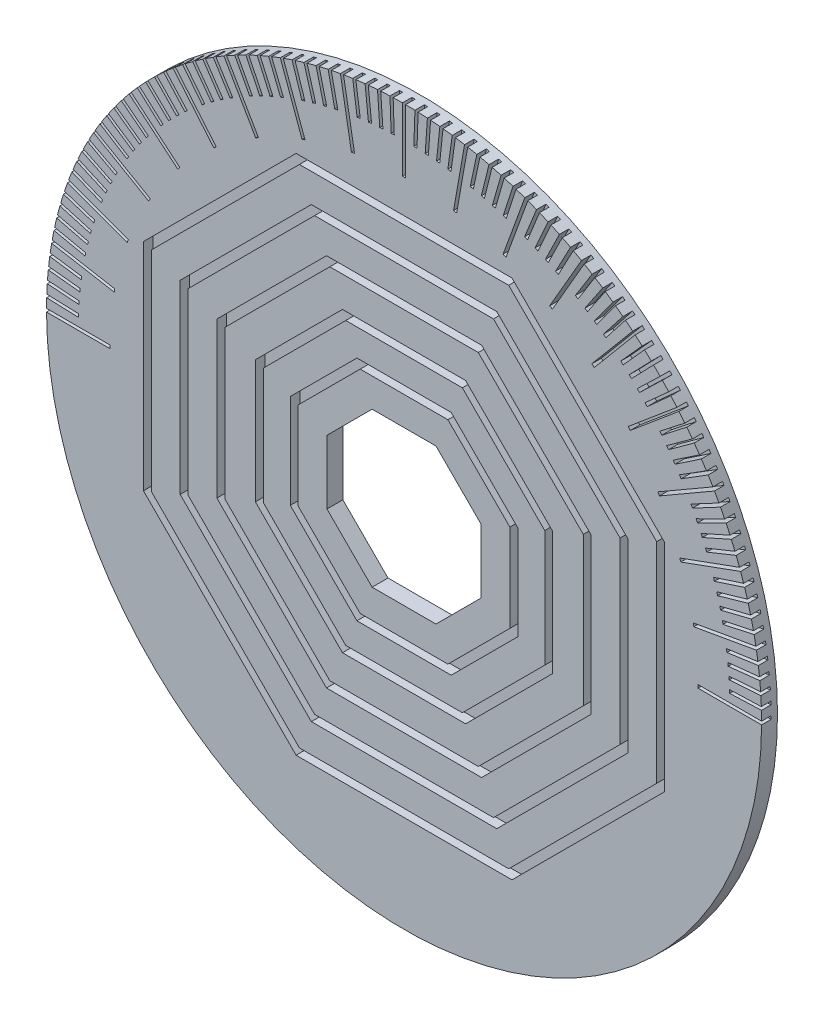
SolidWorks part; units mm, degrees
ref_plane "정면" through (0, 0, 0) normal (0, 0, 1) x (1, 0, 0)
ref_plane "윗면" through (0, 0, 0) normal (0, 1, 0) x (1, 0, 0)
ref_plane "우측면" through (0, 0, 0) normal (1, 0, 0) x (0, 0, -1)
sketch "스케치1" plane through (0, 0, 0) normal (0, 0, 1) x (1, 0, 0)
  circle A0 centre (0, 0) radius 45
  dimension "D1" = 90
extrude "보스-돌출1" add sketch "스케치1" along normal blind 2
sketch "스케치2" plane through (0, 0, 2) normal (0, 0, 1) x (1, 0, 0)
  line L1 (-13.5853, 32.7977) -> (-32.7977, 13.5853)
  line L2 (-32.7977, 13.5853) -> (-32.7977, -13.5853)
  line L3 (-32.7977, -13.5853) -> (-13.5853, -32.7977)
  line L4 (-13.5853, -32.7977) -> (13.5853, -32.7977)
  line L5 (13.5853, -32.7977) -> (32.7977, -13.5853)
  line L6 (32.7977, -13.5853) -> (32.7977, 13.5853)
  line L7 (32.7977, 13.5853) -> (13.5853, 32.7977)
  line L8 (13.5853, 32.7977) -> (-13.5853, 32.7977)
  line L9 (-13.171, 31.7977) -> (-31.7977, 13.171)
  line L10 (-31.7977, 13.171) -> (-31.7977, -13.171)
  line L11 (-31.7977, -13.171) -> (-13.171, -31.7977)
  line L12 (-13.171, -31.7977) -> (13.171, -31.7977)
  line L13 (13.171, -31.7977) -> (31.7977, -13.171)
  line L14 (31.7977, -13.171) -> (31.7977, 13.171)
  line L15 (31.7977, 13.171) -> (13.171, 31.7977)
  line L16 (13.171, 31.7977) -> (-13.171, 31.7977)
  line L18 (55, 0) -> (-55, 0) construction
  circle A0 centre (0, 0) radius 35.5 construction
  dimension "D1" = 71
  dimension "D2" = 1
extrude "컷-돌출1" cut sketch "스케치2" against normal blind 1.2 contours L7 L8 L1 L2 L3 L4 L5 L6 L16 L15 L14 L13 L12 L11 L10 L9
sketch "스케치3" plane through (0, 0, 2) normal (0, 0, 1) x (1, 0, 0)
  line L8 (-31.7977, 13.171) -> (-31.7977, -13.171) construction
  line L9 (11.6718, -28.1783) -> (28.1783, -11.6718)
  line L10 (28.1783, -11.6718) -> (28.1783, 11.6718)
  line L11 (28.1783, 11.6718) -> (11.6718, 28.1783)
  line L12 (11.6718, 28.1783) -> (-11.6718, 28.1783)
  line L13 (-11.6718, 28.1783) -> (-28.1783, 11.6718)
  line L14 (-28.1783, 11.6718) -> (-28.1783, -11.6718)
  line L15 (-28.1783, -11.6718) -> (-11.6718, -28.1783)
  line L16 (-11.6718, -28.1783) -> (11.6718, -28.1783)
  line L17 (11.2576, -27.1783) -> (27.1783, -11.2576)
  line L18 (-9.7584, 23.5589) -> (-23.5589, 9.7584)
  line L19 (-23.5589, 9.7584) -> (-23.5589, -9.7584)
  line L20 (-23.5589, -9.7584) -> (-9.7584, -23.5589)
  line L21 (-9.7584, -23.5589) -> (9.7584, -23.5589)
  line L22 (9.7584, -23.5589) -> (23.5589, -9.7584)
  line L23 (23.5589, -9.7584) -> (23.5589, 9.7584)
  line L24 (23.5589, 9.7584) -> (9.7584, 23.5589)
  line L25 (9.7584, 23.5589) -> (-9.7584, 23.5589)
  line L26 (-7.7493, 18.7086) -> (-18.7086, 7.7493)
  line L27 (-18.7086, 7.7493) -> (-18.7086, -7.7493)
  line L28 (-18.7086, -7.7493) -> (-7.7493, -18.7086)
  line L29 (-7.7493, -18.7086) -> (7.7493, -18.7086)
  line L30 (7.7493, -18.7086) -> (18.7086, -7.7493)
  line L31 (18.7086, -7.7493) -> (18.7086, 7.7493)
  line L32 (18.7086, 7.7493) -> (7.7493, 18.7086)
  line L33 (7.7493, 18.7086) -> (-7.7493, 18.7086)
  line L34 (5.9316, -14.3201) -> (14.3201, -5.9316)
  line L35 (14.3201, -5.9316) -> (14.3201, 5.9316)
  line L36 (14.3201, 5.9316) -> (5.9316, 14.3201)
  line L37 (5.9316, 14.3201) -> (-5.9316, 14.3201)
  line L38 (-5.9316, 14.3201) -> (-14.3201, 5.9316)
  line L39 (-14.3201, 5.9316) -> (-14.3201, -5.9316)
  line L40 (-14.3201, -5.9316) -> (-5.9316, -14.3201)
  line L41 (-5.9316, -14.3201) -> (5.9316, -14.3201)
  line L42 (9.7007, -4.0182) -> (9.7007, 4.0182)
  line L43 (9.7007, 4.0182) -> (4.0182, 9.7007)
  line L44 (4.0182, 9.7007) -> (-4.0182, 9.7007)
  line L45 (-4.0182, 9.7007) -> (-9.7007, 4.0182)
  line L46 (-9.7007, 4.0182) -> (-9.7007, -4.0182)
  line L47 (-9.7007, -4.0182) -> (-4.0182, -9.7007)
  line L48 (-4.0182, -9.7007) -> (4.0182, -9.7007)
  line L49 (4.0182, -9.7007) -> (9.7007, -4.0182)
  line L50 (27.1783, -11.2576) -> (27.1783, 11.2576)
  line L51 (27.1783, 11.2576) -> (11.2576, 27.1783)
  line L52 (11.2576, 27.1783) -> (-11.2576, 27.1783)
  line L53 (-11.2576, 27.1783) -> (-27.1783, 11.2576)
  line L54 (-27.1783, 11.2576) -> (-27.1783, -11.2576)
  line L55 (-27.1783, -11.2576) -> (-11.2576, -27.1783)
  line L56 (-11.2576, -27.1783) -> (11.2576, -27.1783)
  line L57 (-9.3442, 22.5589) -> (-22.5589, 9.3442)
  line L58 (-22.5589, 9.3442) -> (-22.5589, -9.3442)
  line L59 (-22.5589, -9.3442) -> (-9.3442, -22.5589)
  line L60 (-9.3442, -22.5589) -> (9.3442, -22.5589)
  line L61 (9.3442, -22.5589) -> (22.5589, -9.3442)
  line L62 (22.5589, -9.3442) -> (22.5589, 9.3442)
  line L63 (22.5589, 9.3442) -> (9.3442, 22.5589)
  line L64 (9.3442, 22.5589) -> (-9.3442, 22.5589)
  line L65 (-7.3351, 17.7086) -> (-17.7086, 7.3351)
  line L66 (-17.7086, 7.3351) -> (-17.7086, -7.3351)
  line L67 (-17.7086, -7.3351) -> (-7.3351, -17.7086)
  line L68 (-7.3351, -17.7086) -> (7.3351, -17.7086)
  line L69 (7.3351, -17.7086) -> (17.7086, -7.3351)
  line L70 (17.7086, -7.3351) -> (17.7086, 7.3351)
  line L71 (17.7086, 7.3351) -> (7.3351, 17.7086)
  line L72 (7.3351, 17.7086) -> (-7.3351, 17.7086)
  line L73 (5.5174, -13.3201) -> (13.3201, -5.5174)
  line L74 (13.3201, -5.5174) -> (13.3201, 5.5174)
  line L75 (13.3201, 5.5174) -> (5.5174, 13.3201)
  line L76 (5.5174, 13.3201) -> (-5.5174, 13.3201)
  line L77 (-5.5174, 13.3201) -> (-13.3201, 5.5174)
  line L78 (-13.3201, 5.5174) -> (-13.3201, -5.5174)
  line L79 (-13.3201, -5.5174) -> (-5.5174, -13.3201)
  line L80 (-5.5174, -13.3201) -> (5.5174, -13.3201)
  circle A0 centre (0, 0) radius 30.5 construction
  circle A1 centre (0, 0) radius 25.5 construction
  circle A2 centre (0, 0) radius 20.25 construction
  circle A3 centre (0, 0) radius 15.5 construction
  circle A4 centre (0, 0) radius 10.5 construction
  dimension "D1" = 61
  dimension "51" = 51
  dimension "D3" = 40.5
  dimension "D4" = 31
  dimension "D5" = 21
  dimension "D6" = 1
  dimension "D7" = 1
  dimension "D8" = 1
  dimension "D9" = 1
extrude "컷-돌출2" cut sketch "스케치3" against normal blind 1.2 contours L15 L16 L9 L10 L11 L12 L13 L14 L56 L55 L54 L53 L52 L51 L50 L17 | L24 L25 L18 L19 L20 L21 L22 L23 L64 L63 L62 L61 L60 L59 L58 L57 | L32 L33 L26 L27 L28 L29 L30 L31 L72 L71 L70 L69 L68 L67 L66 L65 | L40 L41 L34 L35 L36 L37 L38 L39 L80 L79 L78 L77 L76 L75 L74 L73 | L45 L46 L47 L48 L49 L42 L43 L44
sketch "스케치4" plane through (0, 0, 2) normal (0, 0, 1) x (1, 0, 0)
  line L75 (-32.7977, 13.5853) -> (-32.7977, -13.5853) construction
  line L76 (-45, 0.2) -> (-37, 0.2)
  line L77 (-45, 0.2) -> (-45, -0.2)
  line L78 (-45, -0.2) -> (-37, -0.2)
  line L79 (-37, 0.2) -> (-37, -0.2)
  line L80 (-45, 0) -> (-37, 0) construction
  line L81 (-44.2816, 8.0111) -> (-44.3511, 7.6172)
  line L82 (1.1, 0) -> (-1.1, 0) construction
  line L83 (-44.2816, 8.0111) -> (-36.4032, 6.6219)
  line L84 (-36.4032, 6.6219) -> (-36.4726, 6.228)
  line L85 (-44.3511, 7.6172) -> (-36.4726, 6.228)
  line L86 (-44.3163, 7.8142) -> (-36.4379, 6.425) construction
  line L87 (-42.2178, 15.5788) -> (-42.3546, 15.203)
  line L88 (-42.2178, 15.5788) -> (-34.7002, 12.8427)
  line L89 (-34.7002, 12.8427) -> (-34.837, 12.4668)
  line L90 (-42.3546, 15.203) -> (-34.837, 12.4668)
  line L91 (-42.2862, 15.3909) -> (-34.7686, 12.6547) construction
  line L92 (-38.8711, 22.6732) -> (-39.0711, 22.3268)
  line L93 (-38.8711, 22.6732) -> (-31.9429, 18.6732)
  line L94 (-31.9429, 18.6732) -> (-32.1429, 18.3268)
  line L95 (-39.0711, 22.3268) -> (-32.1429, 18.3268)
  line L96 (-38.9711, 22.5) -> (-32.0429, 18.5) construction
  line L97 (-34.3434, 29.0787) -> (-34.6006, 28.7722)
  line L98 (-34.3434, 29.0787) -> (-28.2151, 23.9364)
  line L99 (-28.2151, 23.9364) -> (-28.4722, 23.6299)
  line L100 (-34.6006, 28.7722) -> (-28.4722, 23.6299)
  line L101 (-34.472, 28.9254) -> (-28.3436, 23.7831) construction
  line L102 (-28.7722, 34.6006) -> (-29.0787, 34.3434)
  line L103 (-28.7722, 34.6006) -> (-23.6299, 28.4722)
  line L104 (-23.6299, 28.4722) -> (-23.9364, 28.2151)
  line L105 (-29.0787, 34.3434) -> (-23.9364, 28.2151)
  line L106 (-28.9254, 34.472) -> (-23.7831, 28.3436) construction
  line L107 (-22.3268, 39.0711) -> (-22.6732, 38.8711)
  line L108 (-22.3268, 39.0711) -> (-18.3268, 32.1429)
  line L109 (-18.3268, 32.1429) -> (-18.6732, 31.9429)
  line L110 (-22.6732, 38.8711) -> (-18.6732, 31.9429)
  line L111 (-22.5, 38.9711) -> (-18.5, 32.0429) construction
  line L112 (-15.203, 42.3546) -> (-15.5788, 42.2178)
  line L113 (-15.203, 42.3546) -> (-12.4668, 34.837)
  line L114 (-12.4668, 34.837) -> (-12.8427, 34.7002)
  line L115 (-15.5788, 42.2178) -> (-12.8427, 34.7002)
  line L116 (-15.3909, 42.2862) -> (-12.6547, 34.7686) construction
  line L117 (-7.6172, 44.3511) -> (-8.0111, 44.2816)
  line L118 (-7.6172, 44.3511) -> (-6.228, 36.4726)
  line L119 (-6.228, 36.4726) -> (-6.6219, 36.4032)
  line L120 (-8.0111, 44.2816) -> (-6.6219, 36.4032)
  line L121 (-7.8142, 44.3163) -> (-6.425, 36.4379) construction
  line L122 (0.2, 45) -> (-0.2, 45)
  line L123 (0.2, 45) -> (0.2, 37)
  line L124 (0.2, 37) -> (-0.2, 37)
  line L125 (-0.2, 45) -> (-0.2, 37)
  line L126 (0, 45) -> (0, 37) construction
  line L127 (8.0111, 44.2816) -> (7.6172, 44.3511)
  line L128 (8.0111, 44.2816) -> (6.6219, 36.4032)
  line L129 (6.6219, 36.4032) -> (6.228, 36.4726)
  line L130 (7.6172, 44.3511) -> (6.228, 36.4726)
  line L131 (7.8142, 44.3163) -> (6.425, 36.4379) construction
  line L132 (15.5788, 42.2178) -> (15.203, 42.3546)
  line L133 (15.5788, 42.2178) -> (12.8427, 34.7002)
  line L134 (12.8427, 34.7002) -> (12.4668, 34.837)
  line L135 (15.203, 42.3546) -> (12.4668, 34.837)
  line L136 (15.3909, 42.2862) -> (12.6547, 34.7686) construction
  line L137 (22.6732, 38.8711) -> (22.3268, 39.0711)
  line L138 (22.6732, 38.8711) -> (18.6732, 31.9429)
  line L139 (18.6732, 31.9429) -> (18.3268, 32.1429)
  line L140 (22.3268, 39.0711) -> (18.3268, 32.1429)
  line L141 (22.5, 38.9711) -> (18.5, 32.0429) construction
  line L142 (29.0787, 34.3434) -> (28.7722, 34.6006)
  line L143 (29.0787, 34.3434) -> (23.9364, 28.2151)
  line L144 (23.9364, 28.2151) -> (23.6299, 28.4722)
  line L145 (28.7722, 34.6006) -> (23.6299, 28.4722)
  line L146 (28.9254, 34.472) -> (23.7831, 28.3436) construction
  line L147 (34.6006, 28.7722) -> (34.3434, 29.0787)
  line L148 (34.6006, 28.7722) -> (28.4722, 23.6299)
  line L149 (28.4722, 23.6299) -> (28.2151, 23.9364)
  line L150 (34.3434, 29.0787) -> (28.2151, 23.9364)
  line L151 (34.472, 28.9254) -> (28.3436, 23.7831) construction
  line L152 (39.0711, 22.3268) -> (38.8711, 22.6732)
  line L153 (39.0711, 22.3268) -> (32.1429, 18.3268)
  line L154 (32.1429, 18.3268) -> (31.9429, 18.6732)
  line L155 (38.8711, 22.6732) -> (31.9429, 18.6732)
  line L156 (38.9711, 22.5) -> (32.0429, 18.5) construction
  line L157 (42.3546, 15.203) -> (42.2178, 15.5788)
  line L158 (42.3546, 15.203) -> (34.837, 12.4668)
  line L159 (34.837, 12.4668) -> (34.7002, 12.8427)
  line L160 (42.2178, 15.5788) -> (34.7002, 12.8427)
  line L161 (42.2862, 15.3909) -> (34.7686, 12.6547) construction
  line L162 (44.3511, 7.6172) -> (44.2816, 8.0111)
  line L163 (44.3511, 7.6172) -> (36.4726, 6.228)
  line L164 (36.4726, 6.228) -> (36.4032, 6.6219)
  line L165 (44.2816, 8.0111) -> (36.4032, 6.6219)
  line L166 (44.3163, 7.8142) -> (36.4379, 6.425) construction
  line L167 (45, -0.2) -> (45, 0.2)
  line L168 (45, -0.2) -> (37, -0.2)
  line L169 (37, -0.2) -> (37, 0.2)
  line L170 (45, 0.2) -> (37, 0.2)
  line L171 (45, 0) -> (37, 0) construction
  point P115 (-2.3849, 0)
  point P122 (0, 0)
  dimension "D1" = 8
  dimension "D2" = 0.4
  dimension "D3" = 45
sketch "스케치6" plane through (0, 0, 2) normal (0, 0, 1) x (1, 0, 0)
  line L0 (-32.7977, 13.5853) -> (-32.7977, -13.5853) construction
  line L1 (-45, 0.2) -> (-41, 0.2)
  line L2 (-45, 0.2) -> (-45, -0.2)
  line L3 (-45, -0.2) -> (-41, -0.2)
  line L4 (-41, 0.2) -> (-41, -0.2)
  line L5 (-45, 0) -> (-41, 0) construction
  line L7 (1.1, 0) -> (-1.1, 0) construction
  line L476 (-44.9656, 1.7704) -> (-44.9796, 1.3706)
  line L501 (-44.9656, 1.7704) -> (-40.968, 1.6308)
  line L526 (-40.968, 1.6308) -> (-40.982, 1.231)
  line L551 (-44.9796, 1.3706) -> (-40.982, 1.231)
  line L576 (-44.9726, 1.5705) -> (-40.975, 1.4309) construction
  line L601 (-44.8764, 3.3386) -> (-44.9043, 2.9395)
  line L626 (-44.8764, 3.3386) -> (-40.8862, 3.0595)
  line L651 (-40.8862, 3.0595) -> (-40.9141, 2.6605)
  line L676 (-44.9043, 2.9395) -> (-40.9141, 2.6605)
  line L701 (-44.8904, 3.139) -> (-40.9001, 2.86) construction
  line L726 (-44.7326, 4.9027) -> (-44.7744, 4.5049)
  line L751 (-44.7326, 4.9027) -> (-40.7545, 4.4846)
  line L776 (-40.7545, 4.4846) -> (-40.7963, 4.0868)
  line L801 (-44.7744, 4.5049) -> (-40.7963, 4.0868)
  line L826 (-44.7535, 4.7038) -> (-40.7754, 4.2857) construction
  line L851 (-44.5342, 6.4608) -> (-44.5899, 6.0647)
  line L876 (-44.5342, 6.4608) -> (-40.5732, 5.9042)
  line L901 (-40.5732, 5.9042) -> (-40.6288, 5.508)
  line L906 (-44.5899, 6.0647) -> (-40.6288, 5.508)
  line L911 (-44.5621, 6.2628) -> (-40.601, 5.7061) construction
  line L916 (-44.2816, 8.0111) -> (-44.3511, 7.6172)
  line L921 (-44.2816, 8.0111) -> (-40.3424, 7.3165)
  line L926 (-40.3424, 7.3165) -> (-40.4118, 6.9226)
  line L931 (-44.3511, 7.6172) -> (-40.4118, 6.9226)
  line L936 (-44.3163, 7.8142) -> (-40.3771, 7.1196) construction
  line L941 (-43.9751, 9.5517) -> (-44.0582, 9.1604)
  line L946 (-43.9751, 9.5517) -> (-40.0625, 8.72)
  line L951 (-40.0625, 8.72) -> (-40.1456, 8.3287)
  line L956 (-44.0582, 9.1604) -> (-40.1456, 8.3287)
  line L961 (-44.0166, 9.356) -> (-40.1041, 8.5244) construction
  line L966 (-43.6149, 11.0805) -> (-43.7117, 10.6924)
  line L971 (-43.6149, 11.0805) -> (-39.7337, 10.1129)
  line L976 (-39.7337, 10.1129) -> (-39.8305, 9.7247)
  line L981 (-43.7117, 10.6924) -> (-39.8305, 9.7247)
  line L986 (-43.6633, 10.8865) -> (-39.7821, 9.9188) construction
  line L991 (-43.2016, 12.5959) -> (-43.3119, 12.2114)
  line L996 (-43.2016, 12.5959) -> (-39.3566, 11.4934)
  line L1001 (-39.3566, 11.4934) -> (-39.4669, 11.1089)
  line L1006 (-43.3119, 12.2114) -> (-39.4669, 11.1089)
  line L1011 (-43.2568, 12.4037) -> (-39.4117, 11.3011) construction
  line L1016 (-42.7357, 14.096) -> (-42.8593, 13.7156)
  line L1021 (-42.7357, 14.096) -> (-38.9315, 12.8599)
  line L1026 (-38.9315, 12.8599) -> (-39.0551, 12.4795)
  line L1031 (-42.8593, 13.7156) -> (-39.0551, 12.4795)
  line L1036 (-42.7975, 13.9058) -> (-38.9933, 12.6697) construction
  line L1041 (-42.2178, 15.5788) -> (-42.3546, 15.203)
  line L1046 (-42.2178, 15.5788) -> (-38.459, 14.2108)
  line L1051 (-38.459, 14.2108) -> (-38.5958, 13.8349)
  line L1056 (-42.3546, 15.203) -> (-38.5958, 13.8349)
  line L1061 (-42.2862, 15.3909) -> (-38.5274, 14.0228) construction
  line L1066 (-41.6484, 17.0427) -> (-41.7982, 16.6719)
  line L1071 (-41.6484, 17.0427) -> (-37.9396, 15.5443)
  line L1076 (-37.9396, 15.5443) -> (-38.0895, 15.1734)
  line L1081 (-41.7982, 16.6719) -> (-38.0895, 15.1734)
  line L1086 (-41.7233, 16.8573) -> (-38.0145, 15.3589) construction
  line L1091 (-41.0282, 18.4859) -> (-41.1909, 18.1204)
  line L1096 (-41.0282, 18.4859) -> (-37.374, 16.8589)
  line L1101 (-37.374, 16.8589) -> (-37.5367, 16.4935)
  line L1106 (-41.1909, 18.1204) -> (-37.5367, 16.4935)
  line L1111 (-41.1095, 18.3031) -> (-37.4554, 16.6762) construction
  line L1116 (-40.3581, 19.9065) -> (-40.5334, 19.5469)
  line L1121 (-40.3581, 19.9065) -> (-36.7629, 18.153)
  line L1126 (-36.7629, 18.153) -> (-36.9382, 17.7935)
  line L1131 (-40.5334, 19.5469) -> (-36.9382, 17.7935)
  line L1136 (-40.4457, 19.7267) -> (-36.8506, 17.9732) construction
  line L1141 (-39.6387, 21.3028) -> (-39.8265, 20.9496)
  line L1146 (-39.6387, 21.3028) -> (-36.107, 19.4249)
  line L1151 (-36.107, 19.4249) -> (-36.2947, 19.0717)
  line L1156 (-39.8265, 20.9496) -> (-36.2947, 19.0717)
  line L1161 (-39.7326, 21.1262) -> (-36.2009, 19.2483) construction
  line L1166 (-38.8711, 22.6732) -> (-39.0711, 22.3268)
  line L1171 (-38.8711, 22.6732) -> (-35.407, 20.6732)
  line L1176 (-35.407, 20.6732) -> (-35.607, 20.3268)
  line L1181 (-39.0711, 22.3268) -> (-35.607, 20.3268)
  line L1186 (-38.9711, 22.5) -> (-35.507, 20.5) construction
  line L1191 (-38.0562, 24.016) -> (-38.2681, 23.6768)
  line L1196 (-38.0562, 24.016) -> (-34.664, 21.8963)
  line L1201 (-34.664, 21.8963) -> (-34.876, 21.5571)
  line L1206 (-38.2681, 23.6768) -> (-34.876, 21.5571)
  line L1211 (-38.1622, 23.8464) -> (-34.77, 21.7267) construction
  line L1216 (-37.1949, 25.3295) -> (-37.4185, 24.9979)
  line L1221 (-37.1949, 25.3295) -> (-33.8787, 23.0927)
  line L1226 (-33.8787, 23.0927) -> (-34.1024, 22.7611)
  line L1231 (-37.4185, 24.9979) -> (-34.1024, 22.7611)
  line L1236 (-37.3067, 25.1637) -> (-33.9905, 22.9269) construction
  line L1241 (-36.2882, 26.6121) -> (-36.5233, 26.2885)
  line L1246 (-36.2882, 26.6121) -> (-33.0521, 24.261)
  line L1251 (-33.0521, 24.261) -> (-33.2873, 23.9374)
  line L1256 (-36.5233, 26.2885) -> (-33.2873, 23.9374)
  line L1261 (-36.4058, 26.4503) -> (-33.1697, 24.0992) construction
  line L1266 (-35.3374, 27.8624) -> (-35.5836, 27.5472)
  line L1271 (-35.3374, 27.8624) -> (-32.1853, 25.3997)
  line L1276 (-32.1853, 25.3997) -> (-32.4316, 25.0845)
  line L1281 (-35.5836, 27.5472) -> (-32.4316, 25.0845)
  line L1286 (-35.4605, 27.7048) -> (-32.3084, 25.2421) construction
  line L1291 (-34.3434, 29.0787) -> (-34.6006, 28.7722)
  line L1296 (-34.3434, 29.0787) -> (-31.2793, 26.5075)
  line L1301 (-31.2793, 26.5075) -> (-31.5364, 26.2011)
  line L1306 (-34.6006, 28.7722) -> (-31.5364, 26.2011)
  line L1311 (-34.472, 28.9254) -> (-31.4078, 26.3543) construction
  line L1316 (-33.3077, 30.2595) -> (-33.5753, 29.9622)
  line L1321 (-33.3077, 30.2595) -> (-30.3351, 27.583)
  line L1326 (-30.3351, 27.583) -> (-30.6028, 27.2857)
  line L1331 (-33.5753, 29.9622) -> (-30.6028, 27.2857)
  line L1336 (-33.4415, 30.1109) -> (-30.4689, 27.4344) construction
  line L1341 (-32.2314, 31.4035) -> (-32.5092, 31.1158)
  line L1346 (-32.2314, 31.4035) -> (-29.354, 28.6249)
  line L1351 (-29.354, 28.6249) -> (-29.6319, 28.3371)
  line L1356 (-32.5092, 31.1158) -> (-29.6319, 28.3371)
  line L1361 (-32.3703, 31.2596) -> (-29.4929, 28.481) construction
  line L1366 (-31.1158, 32.5092) -> (-31.4035, 32.2314)
  line L1371 (-31.1158, 32.5092) -> (-28.3371, 29.6319)
  line L1376 (-28.3371, 29.6319) -> (-28.6249, 29.354)
  line L1381 (-31.4035, 32.2314) -> (-28.6249, 29.354)
  line L1386 (-31.2596, 32.3703) -> (-28.481, 29.4929) construction
  line L1391 (-29.9622, 33.5753) -> (-30.2595, 33.3077)
  line L1396 (-29.9622, 33.5753) -> (-27.2857, 30.6028)
  line L1401 (-27.2857, 30.6028) -> (-27.583, 30.3351)
  line L1406 (-30.2595, 33.3077) -> (-27.583, 30.3351)
  line L1411 (-30.1109, 33.4415) -> (-27.4344, 30.4689) construction
  line L1416 (-28.7722, 34.6006) -> (-29.0787, 34.3434)
  line L1421 (-28.7722, 34.6006) -> (-26.2011, 31.5364)
  line L1426 (-26.2011, 31.5364) -> (-26.5075, 31.2793)
  line L1431 (-29.0787, 34.3434) -> (-26.5075, 31.2793)
  line L1436 (-28.9254, 34.472) -> (-26.3543, 31.4078) construction
  line L1441 (-27.5472, 35.5836) -> (-27.8624, 35.3374)
  line L1446 (-27.5472, 35.5836) -> (-25.0845, 32.4316)
  line L1451 (-25.0845, 32.4316) -> (-25.3997, 32.1853)
  line L1456 (-27.8624, 35.3374) -> (-25.3997, 32.1853)
  line L1461 (-27.7048, 35.4605) -> (-25.2421, 32.3084) construction
  line L1466 (-26.2885, 36.5233) -> (-26.6121, 36.2882)
  line L1471 (-26.2885, 36.5233) -> (-23.9374, 33.2873)
  line L1476 (-23.9374, 33.2873) -> (-24.261, 33.0521)
  line L1481 (-26.6121, 36.2882) -> (-24.261, 33.0521)
  line L1486 (-26.4503, 36.4058) -> (-24.0992, 33.1697) construction
  line L1491 (-24.9979, 37.4185) -> (-25.3295, 37.1949)
  line L1496 (-24.9979, 37.4185) -> (-22.7611, 34.1024)
  line L1501 (-22.7611, 34.1024) -> (-23.0927, 33.8787)
  line L1506 (-25.3295, 37.1949) -> (-23.0927, 33.8787)
  line L1511 (-25.1637, 37.3067) -> (-22.9269, 33.9905) construction
  line L1516 (-23.6768, 38.2681) -> (-24.016, 38.0562)
  line L1521 (-23.6768, 38.2681) -> (-21.5571, 34.876)
  line L1526 (-21.5571, 34.876) -> (-21.8963, 34.664)
  line L1531 (-24.016, 38.0562) -> (-21.8963, 34.664)
  line L1536 (-23.8464, 38.1622) -> (-21.7267, 34.77) construction
  line L1541 (-22.3268, 39.0711) -> (-22.6732, 38.8711)
  line L1546 (-22.3268, 39.0711) -> (-20.3268, 35.607)
  line L1551 (-20.3268, 35.607) -> (-20.6732, 35.407)
  line L1556 (-22.6732, 38.8711) -> (-20.6732, 35.407)
  line L1561 (-22.5, 38.9711) -> (-20.5, 35.507) construction
  line L1566 (-20.9496, 39.8265) -> (-21.3028, 39.6387)
  line L1571 (-20.9496, 39.8265) -> (-19.0717, 36.2947)
  line L1576 (-19.0717, 36.2947) -> (-19.4249, 36.107)
  line L1581 (-21.3028, 39.6387) -> (-19.4249, 36.107)
  line L1586 (-21.1262, 39.7326) -> (-19.2483, 36.2009) construction
  line L1591 (-19.5469, 40.5334) -> (-19.9065, 40.3581)
  line L1596 (-19.5469, 40.5334) -> (-17.7935, 36.9382)
  line L1601 (-17.7935, 36.9382) -> (-18.153, 36.7629)
  line L1606 (-19.9065, 40.3581) -> (-18.153, 36.7629)
  line L1611 (-19.7267, 40.4457) -> (-17.9732, 36.8506) construction
  line L1616 (-18.1204, 41.1909) -> (-18.4859, 41.0282)
  line L1621 (-18.1204, 41.1909) -> (-16.4935, 37.5367)
  line L1626 (-16.4935, 37.5367) -> (-16.8589, 37.374)
  line L1631 (-18.4859, 41.0282) -> (-16.8589, 37.374)
  line L1636 (-18.3031, 41.1095) -> (-16.6762, 37.4554) construction
  line L1641 (-16.6719, 41.7982) -> (-17.0427, 41.6484)
  line L1646 (-16.6719, 41.7982) -> (-15.1734, 38.0895)
  line L1651 (-15.1734, 38.0895) -> (-15.5443, 37.9396)
  line L1656 (-17.0427, 41.6484) -> (-15.5443, 37.9396)
  line L1661 (-16.8573, 41.7233) -> (-15.3589, 38.0145) construction
  line L1666 (-15.203, 42.3546) -> (-15.5788, 42.2178)
  line L1671 (-15.203, 42.3546) -> (-13.8349, 38.5958)
  line L1676 (-13.8349, 38.5958) -> (-14.2108, 38.459)
  line L1681 (-15.5788, 42.2178) -> (-14.2108, 38.459)
  line L1686 (-15.3909, 42.2862) -> (-14.0228, 38.5274) construction
  line L1691 (-13.7156, 42.8593) -> (-14.096, 42.7357)
  line L1696 (-13.7156, 42.8593) -> (-12.4795, 39.0551)
  line L1701 (-12.4795, 39.0551) -> (-12.8599, 38.9315)
  line L1706 (-14.096, 42.7357) -> (-12.8599, 38.9315)
  line L1711 (-13.9058, 42.7975) -> (-12.6697, 38.9933) construction
  line L1712 (-12.2114, 43.3119) -> (-12.5959, 43.2016)
  line L1713 (-12.2114, 43.3119) -> (-11.1089, 39.4669)
  line L1714 (-11.1089, 39.4669) -> (-11.4934, 39.3566)
  line L1715 (-12.5959, 43.2016) -> (-11.4934, 39.3566)
  line L1716 (-12.4037, 43.2568) -> (-11.3011, 39.4117) construction
  line L1717 (-10.6924, 43.7117) -> (-11.0805, 43.6149)
  line L1718 (-10.6924, 43.7117) -> (-9.7247, 39.8305)
  line L1719 (-9.7247, 39.8305) -> (-10.1129, 39.7337)
  line L1720 (-11.0805, 43.6149) -> (-10.1129, 39.7337)
  line L1721 (-10.8865, 43.6633) -> (-9.9188, 39.7821) construction
  line L1722 (-9.1604, 44.0582) -> (-9.5517, 43.9751)
  line L1723 (-9.1604, 44.0582) -> (-8.3287, 40.1456)
  line L1724 (-8.3287, 40.1456) -> (-8.72, 40.0625)
  line L1725 (-9.5517, 43.9751) -> (-8.72, 40.0625)
  line L1726 (-9.356, 44.0166) -> (-8.5244, 40.1041) construction
  line L1727 (-7.6172, 44.3511) -> (-8.0111, 44.2816)
  line L1728 (-7.6172, 44.3511) -> (-6.9226, 40.4118)
  line L1729 (-6.9226, 40.4118) -> (-7.3165, 40.3424)
  line L1730 (-8.0111, 44.2816) -> (-7.3165, 40.3424)
  line L1731 (-7.8142, 44.3163) -> (-7.1196, 40.3771) construction
  line L1732 (-6.0647, 44.5899) -> (-6.4608, 44.5342)
  line L1733 (-6.0647, 44.5899) -> (-5.508, 40.6288)
  line L1734 (-5.508, 40.6288) -> (-5.9042, 40.5732)
  line L1735 (-6.4608, 44.5342) -> (-5.9042, 40.5732)
  line L1736 (-6.2628, 44.5621) -> (-5.7061, 40.601) construction
  line L1737 (-4.5049, 44.7744) -> (-4.9027, 44.7326)
  line L1738 (-4.5049, 44.7744) -> (-4.0868, 40.7963)
  line L1739 (-4.0868, 40.7963) -> (-4.4846, 40.7545)
  line L1740 (-4.9027, 44.7326) -> (-4.4846, 40.7545)
  line L1741 (-4.7038, 44.7535) -> (-4.2857, 40.7754) construction
  line L1742 (-2.9395, 44.9043) -> (-3.3386, 44.8764)
  line L1743 (-2.9395, 44.9043) -> (-2.6605, 40.9141)
  line L1744 (-2.6605, 40.9141) -> (-3.0595, 40.8862)
  line L1745 (-3.3386, 44.8764) -> (-3.0595, 40.8862)
  line L1746 (-3.139, 44.8904) -> (-2.86, 40.9001) construction
  line L1747 (-1.3706, 44.9796) -> (-1.7704, 44.9656)
  line L1748 (-1.3706, 44.9796) -> (-1.231, 40.982)
  line L1749 (-1.231, 40.982) -> (-1.6308, 40.968)
  line L1750 (-1.7704, 44.9656) -> (-1.6308, 40.968)
  line L1751 (-1.5705, 44.9726) -> (-1.4309, 40.975) construction
  line L1752 (0.2, 45) -> (-0.2, 45)
  line L1753 (0.2, 45) -> (0.2, 41)
  line L1754 (0.2, 41) -> (-0.2, 41)
  line L1755 (-0.2, 45) -> (-0.2, 41)
  line L1756 (0, 45) -> (0, 41) construction
  line L1757 (1.7704, 44.9656) -> (1.3706, 44.9796)
  line L1758 (1.7704, 44.9656) -> (1.6308, 40.968)
  line L1759 (1.6308, 40.968) -> (1.231, 40.982)
  line L1760 (1.3706, 44.9796) -> (1.231, 40.982)
  line L1761 (1.5705, 44.9726) -> (1.4309, 40.975) construction
  line L1762 (3.3386, 44.8764) -> (2.9395, 44.9043)
  line L1763 (3.3386, 44.8764) -> (3.0595, 40.8862)
  line L1764 (3.0595, 40.8862) -> (2.6605, 40.9141)
  line L1765 (2.9395, 44.9043) -> (2.6605, 40.9141)
  line L1766 (3.139, 44.8904) -> (2.86, 40.9001) construction
  line L1767 (4.9027, 44.7326) -> (4.5049, 44.7744)
  line L1768 (4.9027, 44.7326) -> (4.4846, 40.7545)
  line L1769 (4.4846, 40.7545) -> (4.0868, 40.7963)
  line L1770 (4.5049, 44.7744) -> (4.0868, 40.7963)
  line L1771 (4.7038, 44.7535) -> (4.2857, 40.7754) construction
  line L1772 (6.4608, 44.5342) -> (6.0647, 44.5899)
  line L1773 (6.4608, 44.5342) -> (5.9042, 40.5732)
  line L1774 (5.9042, 40.5732) -> (5.508, 40.6288)
  line L1775 (6.0647, 44.5899) -> (5.508, 40.6288)
  line L1776 (6.2628, 44.5621) -> (5.7061, 40.601) construction
  line L1777 (8.0111, 44.2816) -> (7.6172, 44.3511)
  line L1778 (8.0111, 44.2816) -> (7.3165, 40.3424)
  line L1779 (7.3165, 40.3424) -> (6.9226, 40.4118)
  line L1780 (7.6172, 44.3511) -> (6.9226, 40.4118)
  line L1781 (7.8142, 44.3163) -> (7.1196, 40.3771) construction
  line L1782 (9.5517, 43.9751) -> (9.1604, 44.0582)
  line L1783 (9.5517, 43.9751) -> (8.72, 40.0625)
  line L1784 (8.72, 40.0625) -> (8.3287, 40.1456)
  line L1785 (9.1604, 44.0582) -> (8.3287, 40.1456)
  line L1786 (9.356, 44.0166) -> (8.5244, 40.1041) construction
  line L1787 (11.0805, 43.6149) -> (10.6924, 43.7117)
  line L1788 (11.0805, 43.6149) -> (10.1129, 39.7337)
  line L1789 (10.1129, 39.7337) -> (9.7247, 39.8305)
  line L1790 (10.6924, 43.7117) -> (9.7247, 39.8305)
  line L1791 (10.8865, 43.6633) -> (9.9188, 39.7821) construction
  line L1792 (12.5959, 43.2016) -> (12.2114, 43.3119)
  line L1793 (12.5959, 43.2016) -> (11.4934, 39.3566)
  line L1794 (11.4934, 39.3566) -> (11.1089, 39.4669)
  line L1795 (12.2114, 43.3119) -> (11.1089, 39.4669)
  line L1796 (12.4037, 43.2568) -> (11.3011, 39.4117) construction
  line L1797 (14.096, 42.7357) -> (13.7156, 42.8593)
  line L1798 (14.096, 42.7357) -> (12.8599, 38.9315)
  line L1799 (12.8599, 38.9315) -> (12.4795, 39.0551)
  line L1800 (13.7156, 42.8593) -> (12.4795, 39.0551)
  line L1801 (13.9058, 42.7975) -> (12.6697, 38.9933) construction
  line L1802 (15.5788, 42.2178) -> (15.203, 42.3546)
  line L1803 (15.5788, 42.2178) -> (14.2108, 38.459)
  line L1804 (14.2108, 38.459) -> (13.8349, 38.5958)
  line L1805 (15.203, 42.3546) -> (13.8349, 38.5958)
  line L1806 (15.3909, 42.2862) -> (14.0228, 38.5274) construction
  line L1807 (17.0427, 41.6484) -> (16.6719, 41.7982)
  line L1808 (17.0427, 41.6484) -> (15.5443, 37.9396)
  line L1809 (15.5443, 37.9396) -> (15.1734, 38.0895)
  line L1810 (16.6719, 41.7982) -> (15.1734, 38.0895)
  line L1811 (16.8573, 41.7233) -> (15.3589, 38.0145) construction
  line L1812 (18.4859, 41.0282) -> (18.1204, 41.1909)
  line L1813 (18.4859, 41.0282) -> (16.8589, 37.374)
  line L1814 (16.8589, 37.374) -> (16.4935, 37.5367)
  line L1815 (18.1204, 41.1909) -> (16.4935, 37.5367)
  line L1816 (18.3031, 41.1095) -> (16.6762, 37.4554) construction
  line L1817 (19.9065, 40.3581) -> (19.5469, 40.5334)
  line L1818 (19.9065, 40.3581) -> (18.153, 36.7629)
  line L1819 (18.153, 36.7629) -> (17.7935, 36.9382)
  line L1820 (19.5469, 40.5334) -> (17.7935, 36.9382)
  line L1821 (19.7267, 40.4457) -> (17.9732, 36.8506) construction
  line L1822 (21.3028, 39.6387) -> (20.9496, 39.8265)
  line L1823 (21.3028, 39.6387) -> (19.4249, 36.107)
  line L1824 (19.4249, 36.107) -> (19.0717, 36.2947)
  line L1825 (20.9496, 39.8265) -> (19.0717, 36.2947)
  line L1826 (21.1262, 39.7326) -> (19.2483, 36.2009) construction
  line L1827 (22.6732, 38.8711) -> (22.3268, 39.0711)
  line L1828 (22.6732, 38.8711) -> (20.6732, 35.407)
  line L1829 (20.6732, 35.407) -> (20.3268, 35.607)
  line L1830 (22.3268, 39.0711) -> (20.3268, 35.607)
  line L1831 (22.5, 38.9711) -> (20.5, 35.507) construction
  line L1832 (24.016, 38.0562) -> (23.6768, 38.2681)
  line L1833 (24.016, 38.0562) -> (21.8963, 34.664)
  line L1834 (21.8963, 34.664) -> (21.5571, 34.876)
  line L1835 (23.6768, 38.2681) -> (21.5571, 34.876)
  line L1836 (23.8464, 38.1622) -> (21.7267, 34.77) construction
  line L1837 (25.3295, 37.1949) -> (24.9979, 37.4185)
  line L1838 (25.3295, 37.1949) -> (23.0927, 33.8787)
  line L1839 (23.0927, 33.8787) -> (22.7611, 34.1024)
  line L1840 (24.9979, 37.4185) -> (22.7611, 34.1024)
  line L1841 (25.1637, 37.3067) -> (22.9269, 33.9905) construction
  line L1842 (26.6121, 36.2882) -> (26.2885, 36.5233)
  line L1843 (26.6121, 36.2882) -> (24.261, 33.0521)
  line L1844 (24.261, 33.0521) -> (23.9374, 33.2873)
  line L1845 (26.2885, 36.5233) -> (23.9374, 33.2873)
  line L1846 (26.4503, 36.4058) -> (24.0992, 33.1697) construction
  line L1847 (27.8624, 35.3374) -> (27.5472, 35.5836)
  line L1848 (27.8624, 35.3374) -> (25.3997, 32.1853)
  line L1849 (25.3997, 32.1853) -> (25.0845, 32.4316)
  line L1850 (27.5472, 35.5836) -> (25.0845, 32.4316)
  line L1851 (27.7048, 35.4605) -> (25.2421, 32.3084) construction
  line L1852 (29.0787, 34.3434) -> (28.7722, 34.6006)
  line L1853 (29.0787, 34.3434) -> (26.5075, 31.2793)
  line L1854 (26.5075, 31.2793) -> (26.2011, 31.5364)
  line L1855 (28.7722, 34.6006) -> (26.2011, 31.5364)
  line L1856 (28.9254, 34.472) -> (26.3543, 31.4078) construction
  line L1857 (30.2595, 33.3077) -> (29.9622, 33.5753)
  line L1858 (30.2595, 33.3077) -> (27.583, 30.3351)
  line L1859 (27.583, 30.3351) -> (27.2857, 30.6028)
  line L1860 (29.9622, 33.5753) -> (27.2857, 30.6028)
  line L1861 (30.1109, 33.4415) -> (27.4344, 30.4689) construction
  line L1862 (31.4035, 32.2314) -> (31.1158, 32.5092)
  line L1863 (31.4035, 32.2314) -> (28.6249, 29.354)
  line L1864 (28.6249, 29.354) -> (28.3371, 29.6319)
  line L1865 (31.1158, 32.5092) -> (28.3371, 29.6319)
  line L1866 (31.2596, 32.3703) -> (28.481, 29.4929) construction
  line L1867 (32.5092, 31.1158) -> (32.2314, 31.4035)
  line L1868 (32.5092, 31.1158) -> (29.6319, 28.3371)
  line L1869 (29.6319, 28.3371) -> (29.354, 28.6249)
  line L1870 (32.2314, 31.4035) -> (29.354, 28.6249)
  line L1871 (32.3703, 31.2596) -> (29.4929, 28.481) construction
  line L1872 (33.5753, 29.9622) -> (33.3077, 30.2595)
  line L1873 (33.5753, 29.9622) -> (30.6028, 27.2857)
  line L1874 (30.6028, 27.2857) -> (30.3351, 27.583)
  line L1875 (33.3077, 30.2595) -> (30.3351, 27.583)
  line L1876 (33.4415, 30.1109) -> (30.4689, 27.4344) construction
  line L1877 (34.6006, 28.7722) -> (34.3434, 29.0787)
  line L1878 (34.6006, 28.7722) -> (31.5364, 26.2011)
  line L1879 (31.5364, 26.2011) -> (31.2793, 26.5075)
  line L1880 (34.3434, 29.0787) -> (31.2793, 26.5075)
  line L1881 (34.472, 28.9254) -> (31.4078, 26.3543) construction
  line L1882 (35.5836, 27.5472) -> (35.3374, 27.8624)
  line L1883 (35.5836, 27.5472) -> (32.4316, 25.0845)
  line L1884 (32.4316, 25.0845) -> (32.1853, 25.3997)
  line L1885 (35.3374, 27.8624) -> (32.1853, 25.3997)
  line L1886 (35.4605, 27.7048) -> (32.3084, 25.2421) construction
  line L1887 (36.5233, 26.2885) -> (36.2882, 26.6121)
  line L1888 (36.5233, 26.2885) -> (33.2873, 23.9374)
  line L1889 (33.2873, 23.9374) -> (33.0521, 24.261)
  line L1890 (36.2882, 26.6121) -> (33.0521, 24.261)
  line L1891 (36.4058, 26.4503) -> (33.1697, 24.0992) construction
  line L1892 (37.4185, 24.9979) -> (37.1949, 25.3295)
  line L1893 (37.4185, 24.9979) -> (34.1024, 22.7611)
  line L1894 (34.1024, 22.7611) -> (33.8787, 23.0927)
  line L1895 (37.1949, 25.3295) -> (33.8787, 23.0927)
  line L1896 (37.3067, 25.1637) -> (33.9905, 22.9269) construction
  line L1897 (38.2681, 23.6768) -> (38.0562, 24.016)
  line L1898 (38.2681, 23.6768) -> (34.876, 21.5571)
  line L1899 (34.876, 21.5571) -> (34.664, 21.8963)
  line L1900 (38.0562, 24.016) -> (34.664, 21.8963)
  line L1901 (38.1622, 23.8464) -> (34.77, 21.7267) construction
  line L1902 (39.0711, 22.3268) -> (38.8711, 22.6732)
  line L1903 (39.0711, 22.3268) -> (35.607, 20.3268)
  line L1904 (35.607, 20.3268) -> (35.407, 20.6732)
  line L1905 (38.8711, 22.6732) -> (35.407, 20.6732)
  line L1906 (38.9711, 22.5) -> (35.507, 20.5) construction
  line L1907 (39.8265, 20.9496) -> (39.6387, 21.3028)
  line L1908 (39.8265, 20.9496) -> (36.2947, 19.0717)
  line L1909 (36.2947, 19.0717) -> (36.107, 19.4249)
  line L1910 (39.6387, 21.3028) -> (36.107, 19.4249)
  line L1911 (39.7326, 21.1262) -> (36.2009, 19.2483) construction
  line L1912 (40.5334, 19.5469) -> (40.3581, 19.9065)
  line L1913 (40.5334, 19.5469) -> (36.9382, 17.7935)
  line L1914 (36.9382, 17.7935) -> (36.7629, 18.153)
  line L1915 (40.3581, 19.9065) -> (36.7629, 18.153)
  line L1916 (40.4457, 19.7267) -> (36.8506, 17.9732) construction
  line L1917 (41.1909, 18.1204) -> (41.0282, 18.4859)
  line L1918 (41.1909, 18.1204) -> (37.5367, 16.4935)
  line L1919 (37.5367, 16.4935) -> (37.374, 16.8589)
  line L1920 (41.0282, 18.4859) -> (37.374, 16.8589)
  line L1921 (41.1095, 18.3031) -> (37.4554, 16.6762) construction
  line L1922 (41.7982, 16.6719) -> (41.6484, 17.0427)
  line L1923 (41.7982, 16.6719) -> (38.0895, 15.1734)
  line L1924 (38.0895, 15.1734) -> (37.9396, 15.5443)
  line L1925 (41.6484, 17.0427) -> (37.9396, 15.5443)
  line L1926 (41.7233, 16.8573) -> (38.0145, 15.3589) construction
  line L1927 (42.3546, 15.203) -> (42.2178, 15.5788)
  line L1928 (42.3546, 15.203) -> (38.5958, 13.8349)
  line L1929 (38.5958, 13.8349) -> (38.459, 14.2108)
  line L1930 (42.2178, 15.5788) -> (38.459, 14.2108)
  line L1931 (42.2862, 15.3909) -> (38.5274, 14.0228) construction
  line L1932 (42.8593, 13.7156) -> (42.7357, 14.096)
  line L1933 (42.8593, 13.7156) -> (39.0551, 12.4795)
  line L1934 (39.0551, 12.4795) -> (38.9315, 12.8599)
  line L1935 (42.7357, 14.096) -> (38.9315, 12.8599)
  line L1936 (42.7975, 13.9058) -> (38.9933, 12.6697) construction
  line L1937 (43.3119, 12.2114) -> (43.2016, 12.5959)
  line L1938 (43.3119, 12.2114) -> (39.4669, 11.1089)
  line L1939 (39.4669, 11.1089) -> (39.3566, 11.4934)
  line L1940 (43.2016, 12.5959) -> (39.3566, 11.4934)
  line L1941 (43.2568, 12.4037) -> (39.4117, 11.3011) construction
  line L1942 (43.7117, 10.6924) -> (43.6149, 11.0805)
  line L1943 (43.7117, 10.6924) -> (39.8305, 9.7247)
  line L1944 (39.8305, 9.7247) -> (39.7337, 10.1129)
  line L1945 (43.6149, 11.0805) -> (39.7337, 10.1129)
  line L1946 (43.6633, 10.8865) -> (39.7821, 9.9188) construction
  line L1947 (44.0582, 9.1604) -> (43.9751, 9.5517)
  line L1948 (44.0582, 9.1604) -> (40.1456, 8.3287)
  line L1949 (40.1456, 8.3287) -> (40.0625, 8.72)
  line L1950 (43.9751, 9.5517) -> (40.0625, 8.72)
  line L1951 (44.0166, 9.356) -> (40.1041, 8.5244) construction
  line L1952 (44.3511, 7.6172) -> (44.2816, 8.0111)
  line L1953 (44.3511, 7.6172) -> (40.4118, 6.9226)
  line L1954 (40.4118, 6.9226) -> (40.3424, 7.3165)
  line L1955 (44.2816, 8.0111) -> (40.3424, 7.3165)
  line L1956 (44.3163, 7.8142) -> (40.3771, 7.1196) construction
  line L1957 (44.5899, 6.0647) -> (44.5342, 6.4608)
  line L1958 (44.5899, 6.0647) -> (40.6288, 5.508)
  line L1959 (40.6288, 5.508) -> (40.5732, 5.9042)
  line L1960 (44.5342, 6.4608) -> (40.5732, 5.9042)
  line L1961 (44.5621, 6.2628) -> (40.601, 5.7061) construction
  line L1962 (44.7744, 4.5049) -> (44.7326, 4.9027)
  line L1963 (44.7744, 4.5049) -> (40.7963, 4.0868)
  line L1964 (40.7963, 4.0868) -> (40.7545, 4.4846)
  line L1965 (44.7326, 4.9027) -> (40.7545, 4.4846)
  line L1966 (44.7535, 4.7038) -> (40.7754, 4.2857) construction
  line L1967 (44.9043, 2.9395) -> (44.8764, 3.3386)
  line L1968 (44.9043, 2.9395) -> (40.9141, 2.6605)
  line L1969 (40.9141, 2.6605) -> (40.8862, 3.0595)
  line L1970 (44.8764, 3.3386) -> (40.8862, 3.0595)
  line L1971 (44.8904, 3.139) -> (40.9001, 2.86) construction
  line L1972 (44.9796, 1.3706) -> (44.9656, 1.7704)
  line L1973 (44.9796, 1.3706) -> (40.982, 1.231)
  line L1974 (40.982, 1.231) -> (40.968, 1.6308)
  line L1975 (44.9656, 1.7704) -> (40.968, 1.6308)
  line L1976 (44.9726, 1.5705) -> (40.975, 1.4309) construction
  line L1977 (45, -0.2) -> (45, 0.2)
  line L1978 (45, -0.2) -> (41, -0.2)
  line L1979 (41, -0.2) -> (41, 0.2)
  line L1980 (45, 0.2) -> (41, 0.2)
  line L1981 (45, 0) -> (41, 0) construction
  point P554 (0, 0)
  point P1088 (0, 0)
  point P1095 (0, 0)
  dimension "D1" = 0.4
  dimension "D2" = 45
  dimension "D3" = 4
extrude "컷-돌출5" cut sketch "스케치6" against normal blind 1.2
extrude "컷-돌출7" cut sketch "스케치4" against normal blind 1.2
sketch "스케치7" plane through (0, 0, 0.8) normal (0, 0, 1) x (1, 0, 0)
  line L8 (4.0182, 9.7007) -> (-4.0182, 9.7007)
  line L9 (-4.0182, 9.7007) -> (-9.7007, 4.0182)
  line L10 (-9.7007, 4.0182) -> (-9.7007, -4.0182)
  line L11 (-9.7007, -4.0182) -> (-4.0182, -9.7007)
  line L12 (-4.0182, -9.7007) -> (4.0182, -9.7007)
  line L13 (4.0182, -9.7007) -> (9.7007, -4.0182)
  line L14 (9.7007, -4.0182) -> (9.7007, 4.0182)
  line L15 (9.7007, 4.0182) -> (4.0182, 9.7007)
  line L16 (4.0182, 9.7007) -> (-4.0182, 9.7007)
  line L17 (-4.0182, 9.7007) -> (-9.7007, 4.0182)
  line L18 (-9.7007, 4.0182) -> (-9.7007, -4.0182)
  line L19 (-9.7007, -4.0182) -> (-4.0182, -9.7007)
  line L20 (-4.0182, -9.7007) -> (4.0182, -9.7007)
  line L21 (4.0182, -9.7007) -> (9.7007, -4.0182)
  line L22 (9.7007, -4.0182) -> (9.7007, 4.0182)
  line L23 (9.7007, 4.0182) -> (4.0182, 9.7007)
  dimension "D1" = 0
extrude "컷-돌출8" cut sketch "스케치7" against normal through all
